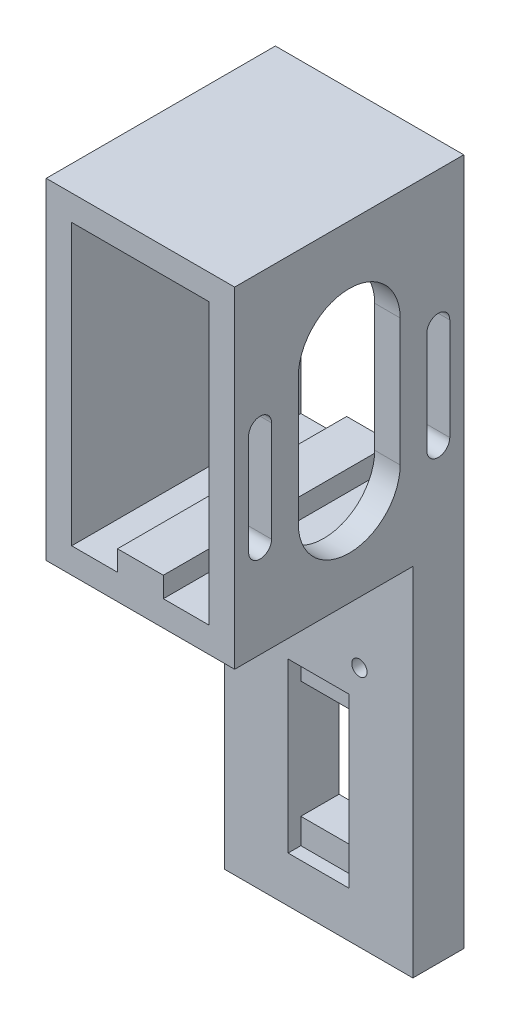
SolidWorks part; units mm, degrees
ref_plane "Plan de face" through (0, 0, 0) normal (0, 0, 1) x (1, 0, 0)
ref_plane "Plan de dessus" through (0, 0, 0) normal (0, 1, 0) x (1, 0, 0)
ref_plane "Plan de droite" through (0, 0, 0) normal (1, 0, 0) x (0, 0, -1)
sketch "Esquisse1" plane through (0, 0, 0) normal (0, 0, 1) x (1, 0, 0)
  line L0 (-40.1057, 31.5871) -> (-35.1057, 31.5871)
  line L2 (-40.1057, 31.5871) -> (-40.1057, -28.4129)
  line L3 (-40.1057, -28.4129) -> (-3.1057, -28.4129)
  line L4 (-3.1057, 31.5871) -> (-3.1057, -28.4129)
  line L5 (-35.1057, 31.5871) -> (-35.1057, -23.4129)
  line L6 (-35.1057, -23.4129) -> (-26.1057, -23.4129)
  line L7 (-26.1057, -23.4129) -> (-26.1057, -19.4129)
  line L8 (-26.1057, -19.4129) -> (-17.1057, -19.4129)
  line L9 (-17.1057, -19.4129) -> (-17.1057, -23.4129)
  line L10 (-17.1057, -23.4129) -> (-8.1057, -23.4129)
  line L11 (-8.1057, -23.4129) -> (-8.1057, 31.5871)
  line L12 (-8.1057, 31.5871) -> (-3.1057, 31.5871)
  dimension "D1" = 37
  dimension "D2" = 60
  dimension "D3" = 5
  dimension "D4" = 5
  dimension "D5" = 9
  dimension "D6" = 9
  dimension "D7" = 5
  dimension "D8" = 4
  dimension "D9" = 4
  dimension "D10" = 9
  dimension "D11" = 60
extrude "Boss.-Extru.1" add sketch "Esquisse1" along normal blind 45
sketch "Esquisse2" plane through (-3.1057, 0, 0) normal (1, 0, 0) x (0, 0, -1)
  line L0 (-22.5, 31.5871) -> (-22.5, -28.4129) construction
  line L1 (-45, 31.5871) -> (0, 31.5871) construction
  line L2 (-45, -28.4129) -> (0, -28.4129) construction
  line L3 (-22.5, 15.0871) -> (-22.5, -9.9129) construction
  line L4 (-12.5, 15.0871) -> (-12.5, -9.9129)
  line L5 (-32.5, 15.0871) -> (-32.5, -9.9129)
  line L6 (-53.101, 2.5871) -> (12.8547, 2.5871) construction
  line L7 (-40, 15.1582) -> (-40, -20.8265) construction
  line L10 (-40, 9.8775) -> (-40, -9.9129) construction
  line L11 (-5, 16.6338) -> (-5, -20.8265) construction
  line L12 (-37.75, 9.8775) -> (-37.75, -9.9129)
  line L13 (-42.25, 9.8775) -> (-42.25, -9.9129)
  line L14 (-37.75, -9.9129) -> (20.4864, -9.9129) construction
  line L15 (20.4864, -9.9129) -> (20.4864, 9.8775) construction
  line L16 (20.4864, 9.8775) -> (-68.9251, 9.8775) construction
  line L17 (-5, 9.8775) -> (-5, -10.1225) construction
  line L18 (-2.75, 9.8775) -> (-2.75, -10.1225)
  line L19 (-7.25, 9.8775) -> (-7.25, -10.1225)
  arc A0 (-12.5, 15.0871) -> (-32.5, 15.0871) centre (-22.5, 15.0871) ccw
  arc A1 (-32.5, -9.9129) -> (-12.5, -9.9129) centre (-22.5, -9.9129) ccw
  arc A4 (-37.75, 9.8775) -> (-42.25, 9.8775) centre (-40, 9.8775) ccw
  arc A5 (-42.25, -9.9129) -> (-37.75, -9.9129) centre (-40, -9.9129) ccw
  arc A6 (-2.75, 9.8775) -> (-7.25, 9.8775) centre (-5, 9.8775) ccw
  arc A7 (-7.25, -10.1225) -> (-2.75, -10.1225) centre (-5, -10.1225) ccw
  point P8 (-22.5, 2.5871)
  point P17 (-40, -0.0177)
  point P33 (-5, -0.1225)
  dimension "D1" = 20
  dimension "D3" = 16.5
  dimension "D2" = 25
  dimension "D4" = 35
  dimension "D5" = 5.25
  dimension "D6" = 4.5
  dimension "D7" = 4.5
  dimension "D8" = 5.25
extrude "Enlèv. mat.-Extru.1" cut sketch "Esquisse2" against normal up to surface (5 mm away) up to face at (-8.1057, 4.0871, 22.5)
sketch "Esquisse4" plane through (0, 31.5871, 0) normal (0, 1, 0) x (1, 0, 0)
  line L0 (-40.1057, -45) -> (-40.1057, 0) construction
  line L1 (-40.1057, 0) -> (-3.1057, 0)
  line L2 (-40.1057, 0) -> (-40.1057, -45)
  line L3 (-40.1057, -45) -> (-3.1057, -45)
  line L4 (-3.1057, 0) -> (-3.1057, -45)
extrude "Boss.-Extru.2" add sketch "Esquisse4" along normal blind 5
sketch "Esquisse5" plane through (0, -28.4129, 0) normal (0, -1, 0) x (1, 0, 0)
  line L0 (-3.1057, 45) -> (-3.1057, 0) construction
  line L1 (-40.1057, 0) -> (-3.1057, 0)
  line L2 (-40.1057, 0) -> (-40.1057, 10)
  line L3 (-40.1057, 10) -> (-3.1057, 10)
  line L4 (-3.1057, 0) -> (-3.1057, 10)
  dimension "D1" = 10
extrude "Boss.-Extru.3" add sketch "Esquisse5" along normal blind 70
sketch "Esquisse6" plane through (-40.1057, 0, 0) normal (-1, 0, 0) x (0, 0, 1)
  line L0 (45, -23.4129) -> (0, -23.4129) construction
  line L1 (45, 36.5871) -> (45, -28.4129) construction
  line L2 (0, 36.5871) -> (0, -98.4129) construction
  line L3 (45, -28.4129) -> (10, -28.4129) construction
  line L4 (15, -23.4129) -> (15, 3.3301) construction
  circle A0 centre (15, -18.4129) radius 1
  circle A1 centre (15, -8.9129) radius 1
  dimension "D2" = 2
  dimension "D5" = 2
  dimension "D1" = 5
  dimension "D3" = 5
  dimension "D4" = 9.5
  dimension "D6" = 15
extrude "Enlèv. mat.-Extru.2" cut sketch "Esquisse6" against normal blind 10
chamfer "Chanfrein2" distance 1 angle 45 2 edges at (-35.1057, -19.4129, 15) (-35.1057, -9.9129, 15)
sketch "Esquisse7" plane through (0, 0, 10) normal (0, 0, 1) x (1, 0, 0)
  line L0 (-21.6057, -28.4129) -> (-21.6057, -98.4129) construction
  line L1 (-3.1057, -28.4129) -> (-40.1057, -28.4129) construction
  line L2 (-3.1057, -98.4129) -> (-40.1057, -98.4129) construction
  line L3 (-27.6057, -84.4129) -> (-15.6057, -84.4129)
  line L4 (-40.1057, -98.4129) -> (-40.1057, -28.4129) construction
  line L5 (-40.1057, -78.4129) -> (-3.1057, -78.4129) construction
  line L6 (-3.1057, -98.4129) -> (-3.1057, -28.4129) construction
  line L7 (-15.6057, -84.4129) -> (-15.6057, -61.4129)
  line L8 (-15.6057, -61.4129) -> (-27.6057, -61.4129)
  line L9 (-27.6057, -61.4129) -> (-27.6057, -84.4129)
  point P15 (-21.6057, -84.4129)
  dimension "D1" = 50
  dimension "D2" = 12
  dimension "D3" = 23
  dimension "D4" = 6
extrude "Enlèv. mat.-Extru.3" cut sketch "Esquisse7" against normal blind 10
sketch "Esquisse8" plane through (0, 0, 10) normal (0, 0, 1) x (1, 0, 0)
  line L1 (-27.6057, -61.4129) -> (-15.6057, -61.4129)
  line L2 (-27.6057, -61.4129) -> (-27.6057, -56.4129)
  line L3 (-27.6057, -56.4129) -> (-15.6057, -56.4129)
  line L4 (-15.6057, -61.4129) -> (-15.6057, -56.4129)
  line L5 (-27.6057, -84.4129) -> (-15.6057, -84.4129)
  line L6 (-27.6057, -84.4129) -> (-27.6057, -89.4129)
  line L7 (-27.6057, -89.4129) -> (-15.6057, -89.4129)
  line L8 (-15.6057, -84.4129) -> (-15.6057, -89.4129)
  dimension "D1" = 12
  dimension "D2" = 12
  dimension "D3" = 5
  dimension "D4" = 5
extrude "Enlèv. mat.-Extru.4" cut sketch "Esquisse8" against normal blind 2.5
sketch "Esquisse10" plane through (0, 0, 10) normal (0, 0, 1) x (1, 0, 0)
  line L0 (-40.1057, -35.9129) -> (-3.1057, -35.9129) construction
  line L1 (-40.1057, -98.4129) -> (-40.1057, -28.4129) construction
  line L2 (-3.1057, -98.4129) -> (-3.1057, -28.4129) construction
  line L3 (-29.6057, -35.9129) -> (-29.6057, -50.9129) construction
  line L4 (-40.1057, -50.9129) -> (-3.1057, -50.9129) construction
  line L5 (-13.6057, -35.9129) -> (-13.6057, -50.9129) construction
  line L6 (-3.1057, -28.4129) -> (-40.1057, -28.4129) construction
  circle A0 centre (-29.6057, -35.9129) radius 1.5
  circle A1 centre (-29.6057, -50.9129) radius 1.5
  circle A2 centre (-13.6057, -50.9129) radius 1.5
  circle A3 centre (-13.6057, -35.9129) radius 1.5
  dimension "D1" = 3
  dimension "D2" = 3
  dimension "D3" = 3
  dimension "D4" = 3
  dimension "D5" = 16
  dimension "D6" = 10.5
  dimension "D7" = 10.5
  dimension "D8" = 7.5
  dimension "D9" = 15
extrude "Enlèv. mat.-Extru.5" cut sketch "Esquisse10" against normal blind 10
